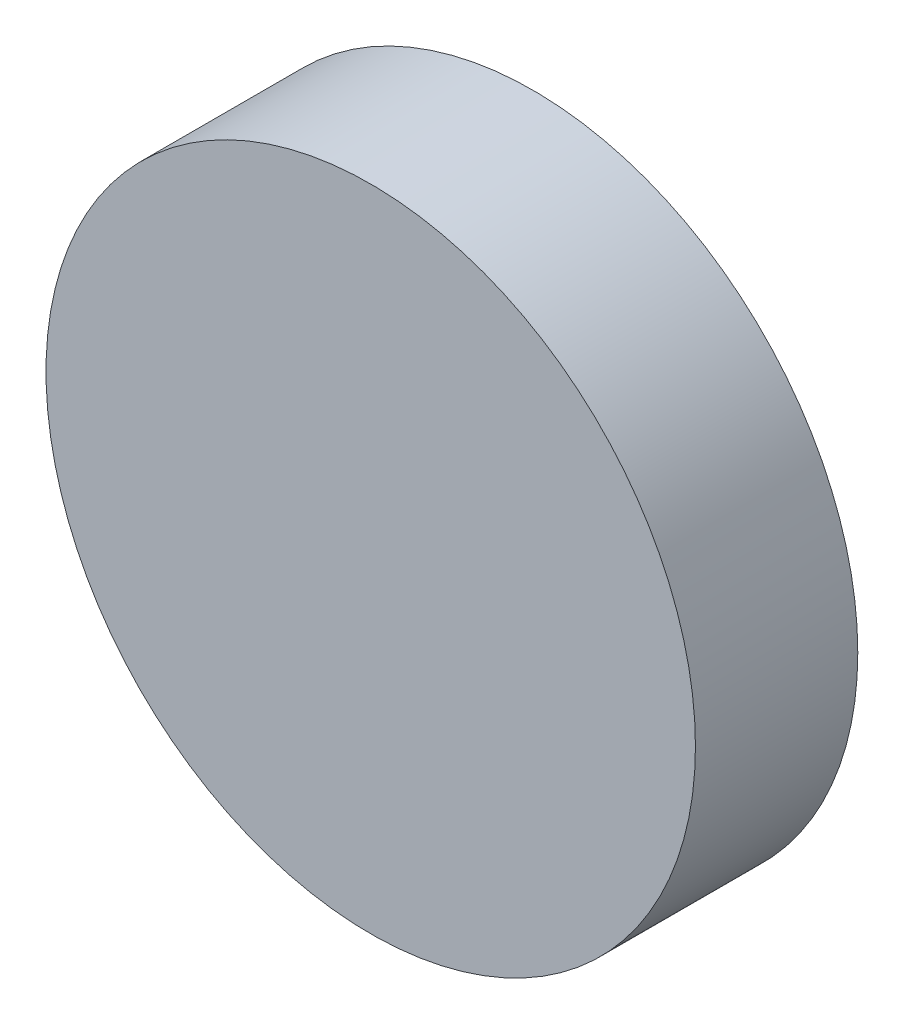
SolidWorks part; units mm, degrees
ref_plane "Front Plane" through (0, 0, 0) normal (0, 0, 1) x (1, 0, 0)
ref_plane "Top Plane" through (0, 0, 0) normal (0, 1, 0) x (1, 0, 0)
ref_plane "Right Plane" through (0, 0, 0) normal (1, 0, 0) x (0, 0, -1)
sketch "Sketch1" plane through (0, 0, 0) normal (0, 0, 1) x (1, 0, 0)
  circle A0 centre (0, 0) radius 63.5
  dimension "D1" = 127
extrude "Boss-Extrude1" add sketch "Sketch1" along normal blind 31.75
sketch "Sketch2" plane through (0, 0, 0) normal (0, 0, -1) x (-1, 0, 0)
  circle A0 centre (0, 0) radius 57.15
  circle A1 centre (0, 0) radius 55.5625
  dimension "D1" = 114.3
  dimension "D2" = 111.125
extrude "Cut-Extrude1" cut sketch "Sketch2" against normal blind 3.175
